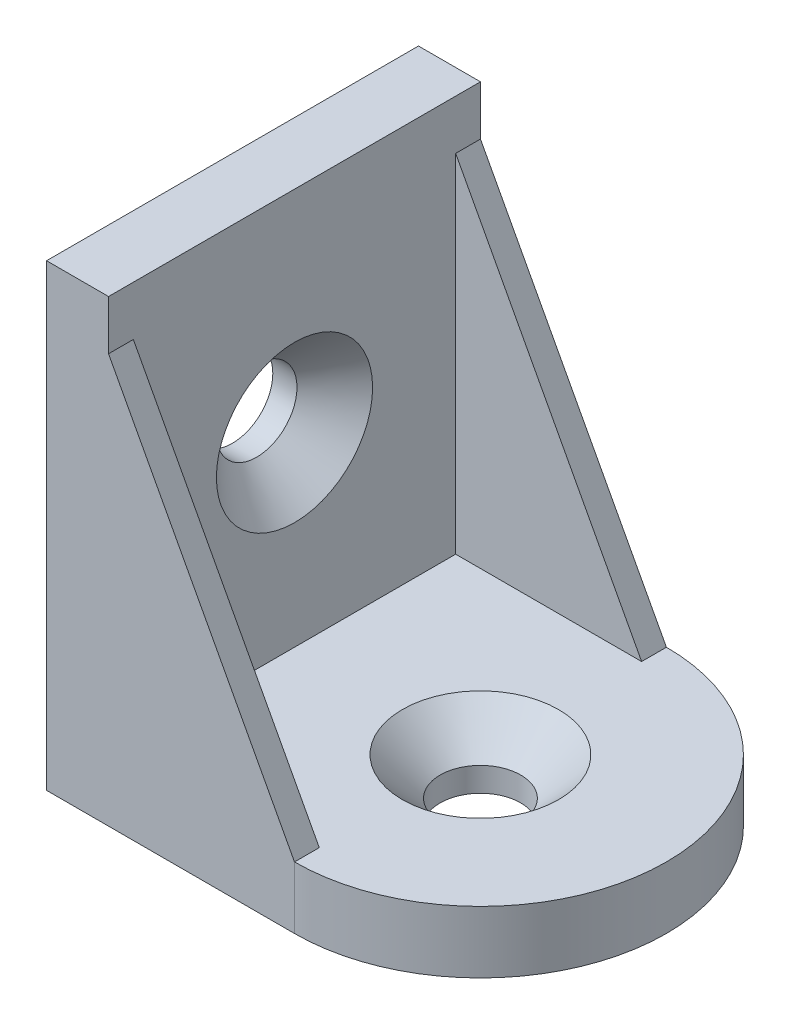
SolidWorks part; units mm, degrees
material "Алюминиевый сплав"
ref_plane "Спереди" through (0, 0, 0) normal (0, 0, 1) x (1, 0, 0)
ref_plane "Сверху" through (0, 0, 0) normal (0, 1, 0) x (1, 0, 0)
ref_plane "Справа" through (0, 0, 0) normal (1, 0, 0) x (0, 0, -1)
sketch "Эскиз1" plane through (0, 0, 0) normal (0, 0, 1) x (1, 0, 0)
  line L0 (0, 37) -> (0, 0)
  line L1 (0, 0) -> (35, 0)
  line L2 (35, 0) -> (35, 5)
  line L4 (5, 37) -> (0, 37)
  line L5 (5, 37) -> (5, 5)
  line L6 (5, 5) -> (35, 5)
  dimension "D1" = 37
  dimension "D2" = 5
  dimension "D3" = 35
extrude "Бобышка-Вытянуть1" add sketch "Эскиз1" along normal mid plane 30
sketch "Эскиз5" plane through (0, 5, 0) normal (0, 1, 0) x (1, 0, 0)
  line L0 (35, 15) -> (5, 15) construction
  line L1 (35, -15) -> (5, -15) construction
  line L2 (35, -15) -> (35, 15) construction
  line L3 (20, 15) -> (35, 15)
  line L4 (35, 15) -> (35, 0)
  line L5 (35, 0) -> (35, -15)
  line L6 (35, -15) -> (20, -15)
  arc A0 (20, 15) -> (20, -15) centre (20, 0) cw
  line M1 (35, 15) -> (5, 15)
  line M3 (5, -15) -> (35, -15)
  line M4 (35, -15) -> (35, 15)
extrude "Вырез-Вытянуть2" cut sketch "Эскиз5" against normal through all contours A0 M1 M4 | A0 M4 M3
sketch "Эскиз2" plane through (0, 0, 15) normal (0, 0, 1) x (1, 0, 0)
  line L0 (5, 33) -> (20, 5)
  line L1 (20, 5) -> (5, 5)
  line L2 (5, 5) -> (5, 33)
  line L3 (5, 5) -> (5, 37) construction
  dimension "D1" = 4
extrude "Бобышка-Вытянуть2" add sketch "Эскиз2" against normal blind 2
mirror "Зеркальное отражение2" about plane through (0, 0, 0) normal (0, 0, 1) of "Бобышка-Вытянуть2"
hole_wizard "Зенковка для винта с полупотайной головкой M61" positions "Эскиз6" profile "Эскиз8" countersink size "M6" standard "ISO"
sketch "Эскиз6" plane through (0, 5, 0) normal (0, 1, 0) x (1, 0, 0)
  point P0 (20, 0)
sketch "Эскиз8" plane through (20, 5, 0) normal (1, 0, 0) x (0, 0, 1)
  line L0 (0, 0) -> (0, 11.2028)
  line L1 (0, 11.2028) -> (3.25, 9.25)
  line L2 (3.25, 9.25) -> (3.25, 3.05)
  line L3 (3.25, 3.05) -> (6.3, 0)
  line L5 (6.3, 0) -> (0, 0)
  line L6 (-3.25, 3.05) -> (-6.3, 0) construction
  line L10 (0, 11.2028) -> (-3.25, 9.25) construction
  line L11 (0, -6.35) -> (0, 107.95) construction
  dimension "Диаметр отверстия" = 6.5
  dimension "Глубина отверстия" = 9.25
  dimension "Диаметр передней зенковки" = 12.6
  dimension "Угол передней зенковки" = 90
  dimension "Угол заточки сверла" = 118
ref_plane "Плоскость1" through (0, 0, 0) normal (-0.7071, 0.7071, 0) x (0.7071, 0.7071, 0)
mirror "Зеркальное отражение3" about plane through (0, 0, 0) normal (-0.7071, 0.7071, 0) of "Зенковка для винта с полупотайной головкой M61"
